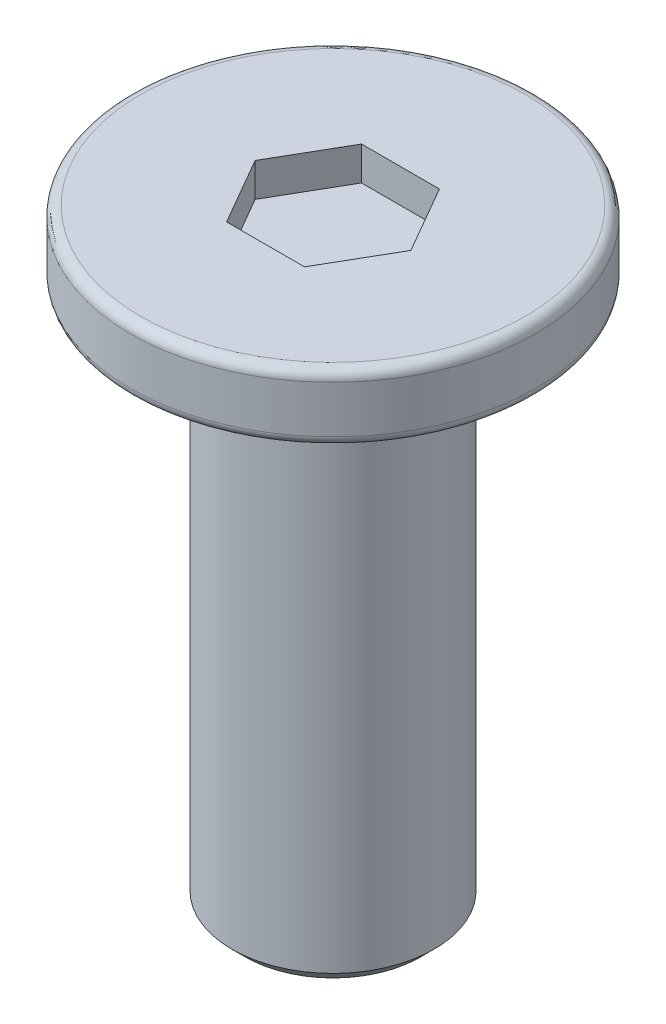
SolidWorks part; units mm, degrees
ref_plane "前视基准面" through (0, 0, 0) normal (0, 0, 1) x (1, 0, 0)
ref_plane "上视基准面" through (0, 0, 0) normal (0, 1, 0) x (1, 0, 0)
ref_plane "右视基准面" through (0, 0, 0) normal (1, 0, 0) x (0, 0, -1)
sketch "草图1" plane through (0, 0, 0) normal (0, 1, 0) x (1, 0, 0)
  circle A0 centre (0, 0) radius 3
  dimension "D1" = 6
extrude "凸台-拉伸1" add sketch "草图1" along normal blind 1
sketch "草图2" plane through (0, 0, 0) normal (0, -1, 0) x (1, 0, 0)
  circle A0 centre (0, 0) radius 1.5
  dimension "D1" = 3
extrude "凸台-拉伸2" add sketch "草图2" along normal blind 8
fillet "圆角1" radius 0.15 2 edges at (0, 0, 3) (0, 1, 3)
chamfer "倒角1" distance 0.2 angle 45 1 edges at (0, -8, -1.5)
sketch "草图3" plane through (0, 1, 0) normal (0, 1, 0) x (1, 0, 0)
  line L1 (1.1547, 0) -> (0.5774, 1)
  line L2 (0.5774, 1) -> (-0.5774, 1)
  line L3 (-0.5774, 1) -> (-1.1547, 0)
  line L4 (-1.1547, 0) -> (-0.5774, -1)
  line L5 (-0.5774, -1) -> (0.5774, -1)
  line L6 (0.5774, -1) -> (1.1547, 0)
  circle A0 centre (0, 0) radius 1 construction
  dimension "D1" = 2
extrude "切除-拉伸1" cut sketch "草图3" against normal blind 0.5
